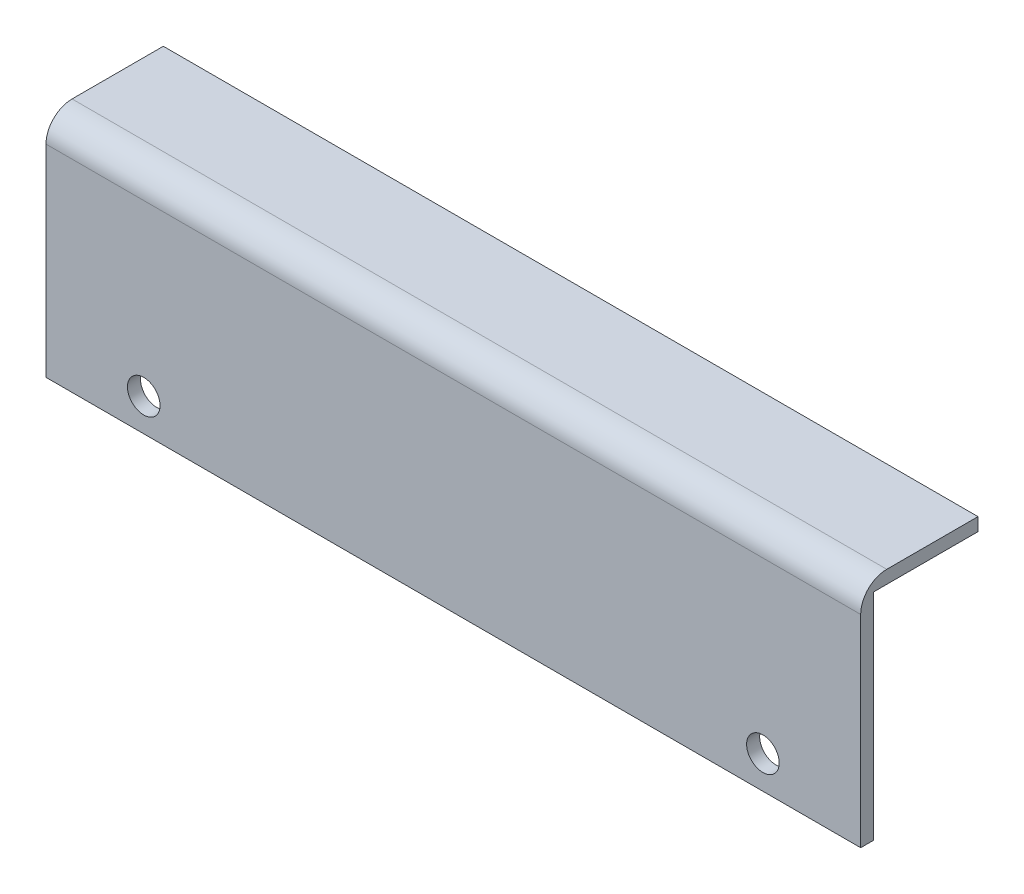
SolidWorks part; units mm, degrees
ref_plane "Front Plane" through (0, 0, 0) normal (0, 0, 1) x (1, 0, 0)
ref_plane "Top Plane" through (0, 0, 0) normal (0, 1, 0) x (1, 0, 0)
ref_plane "Right Plane" through (0, 0, 0) normal (1, 0, 0) x (0, 0, -1)
sketch "Sketch1" plane through (0, 0, 0) normal (1, 0, 0) x (0, 0, -1)
  line L0 (1.1416, 16.7868) -> (17.1416, 16.7868)
  line L3 (-0.8584, -16.2132) -> (1.1416, -16.2132)
  line L4 (1.1416, 16.7868) -> (1.1416, -16.2132)
  line L5 (-0.8584, 18.7868) -> (-0.8584, -16.2132)
  line L7 (-0.8584, 18.7868) -> (17.1416, 18.7868)
  line L10 (17.1416, 18.7868) -> (17.1416, 16.7868)
  point P0 (0, 0)
  dimension "D1" = 35
  dimension "D2" = 18
  dimension "D3" = 2
  dimension "D4" = 2
extrude "Boss-Extrude1" add sketch "Sketch1" along normal blind 125
fillet "Fillet1" radius 4 1 edges at (62.5, 18.7868, 0.8584)
sketch "Sketch2" plane through (0, 0, -1.1416) normal (0, 0, -1) x (-1, 0, 0)
  line L0 (-125, -16.2132) -> (0, -16.2132) construction
  line L2 (0, -16.2132) -> (0, 16.7868) construction
  line L3 (-125, -16.2132) -> (-125, 16.7868) construction
  circle A0 centre (-110, -11.2132) radius 2.5
  circle A1 centre (-15, -11.2132) radius 2.5
  dimension "D1" = 5
  dimension "D2" = 5
  dimension "D3" = 15
  dimension "D4" = 15
extrude "Cut-Extrude1" cut sketch "Sketch2" against normal blind 125
